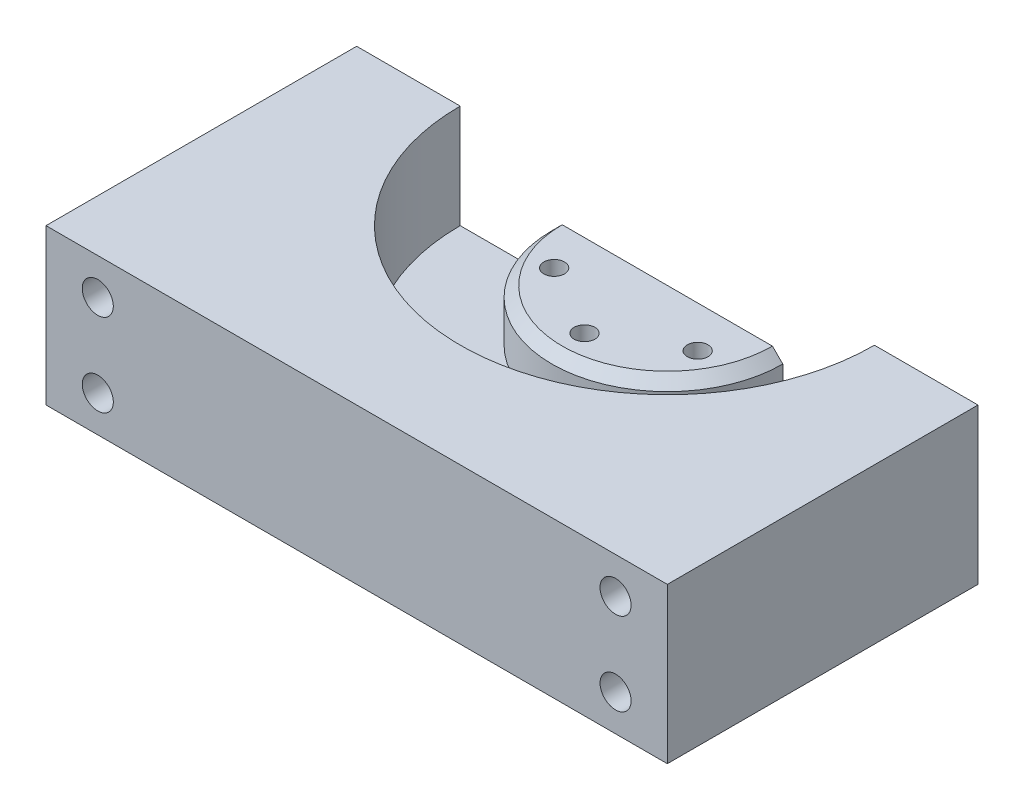
SolidWorks part; units mm, degrees
ref_plane "Plan de face" through (0, 0, 0) normal (0, 0, 1) x (1, 0, 0)
ref_plane "Plan de dessus" through (0, 0, 0) normal (0, 1, 0) x (1, 0, 0)
ref_plane "Plan de droite" through (0, 0, 0) normal (1, 0, 0) x (0, 0, -1)
sketch "Esquisse1" plane through (0, 0, 0) normal (0, 1, 0) x (1, 0, 0)
  line L1 (-60, -30) -> (60, -30)
  line L2 (-60, -30) -> (-60, 30)
  line L3 (-60, 30) -> (60, 30)
  line L4 (60, -30) -> (60, 30)
  line L5 (-60, -30) -> (60, 30) construction
  line L6 (-60, 30) -> (60, -30) construction
  point P0 (0, 0)
  dimension "D1" = 120
  dimension "D2" = 60
extrude "Boss.-Extru.1" add sketch "Esquisse1" along normal blind 10
sketch "Esquisse2" plane through (0, 10, 0) normal (0, 1, 0) x (1, 0, 0)
  line L0 (60, 30) -> (-60, 30) construction
  line L1 (-40, 30) -> (-60, 30)
  line L2 (-60, 30) -> (-60, -30)
  line L3 (-60, -30) -> (60, -30)
  line L4 (60, -30) -> (60, 30)
  line L5 (60, 30) -> (40, 30)
  arc A0 (-40, 30) -> (40, 30) centre (0, 30) ccw
  point P6 (0, 30)
  dimension "D1" = 80
extrude "Boss.-Extru.2" add sketch "Esquisse2" along normal blind 20
sketch "Esquisse3" plane through (0, 10, 0) normal (0, 1, 0) x (1, 0, 0)
  line L0 (40, 30) -> (-40, 30) construction
  line L1 (-22.3, 30) -> (22.3, 30)
  arc A0 (-22.3, 30) -> (22.3, 30) centre (0, 30) ccw
  point P3 (0, 30)
  dimension "D1" = 44.6
extrude "Boss.-Extru.3" add sketch "Esquisse3" along normal blind 10
chamfer "Chanfrein1" distance 2 angle 45 1 edges at (0, 20, -7.7)
sketch "Esquisse4" plane through (0, 0, -30) normal (0, 0, -1) x (-1, 0, 0)
  line L0 (-50, 23) -> (50, 23) construction
  line L1 (0, 0) -> (0, 23) construction
  line L2 (-50, 23) -> (-50, 7) construction
  line L3 (50, 23) -> (50, 7) construction
  circle A0 centre (-50, 23) radius 3
  circle A1 centre (50, 23) radius 3
  circle A2 centre (-50, 7) radius 3
  circle A3 centre (50, 7) radius 3
  dimension "D2" = 6
  dimension "D1" = 100
  dimension "D3" = 23
  dimension "D4" = 16
extrude "Enlèv. mat.-Extru.1" cut sketch "Esquisse4" against normal up to next
sketch "Esquisse5" plane through (0, 20, 0) normal (0, 1, 0) x (1, 0, 0)
  line L0 (0, 14) -> (0, 30) construction
  line L1 (20.3, 30) -> (-20.3, 30) construction
  line L2 (0, 30) -> (-13.8564, 22) construction
  line L3 (0, 30) -> (13.8564, 22) construction
  circle A0 centre (0, 14) radius 2
  circle A2 centre (-13.8564, 22) radius 2
  circle A3 centre (13.8564, 22) radius 2
  dimension "D1" = 4
  dimension "D2" = 16
  dimension "D3" = 60
  dimension "D4" = 60
extrude "Enlèv. mat.-Extru.2" cut sketch "Esquisse5" against normal up to next
